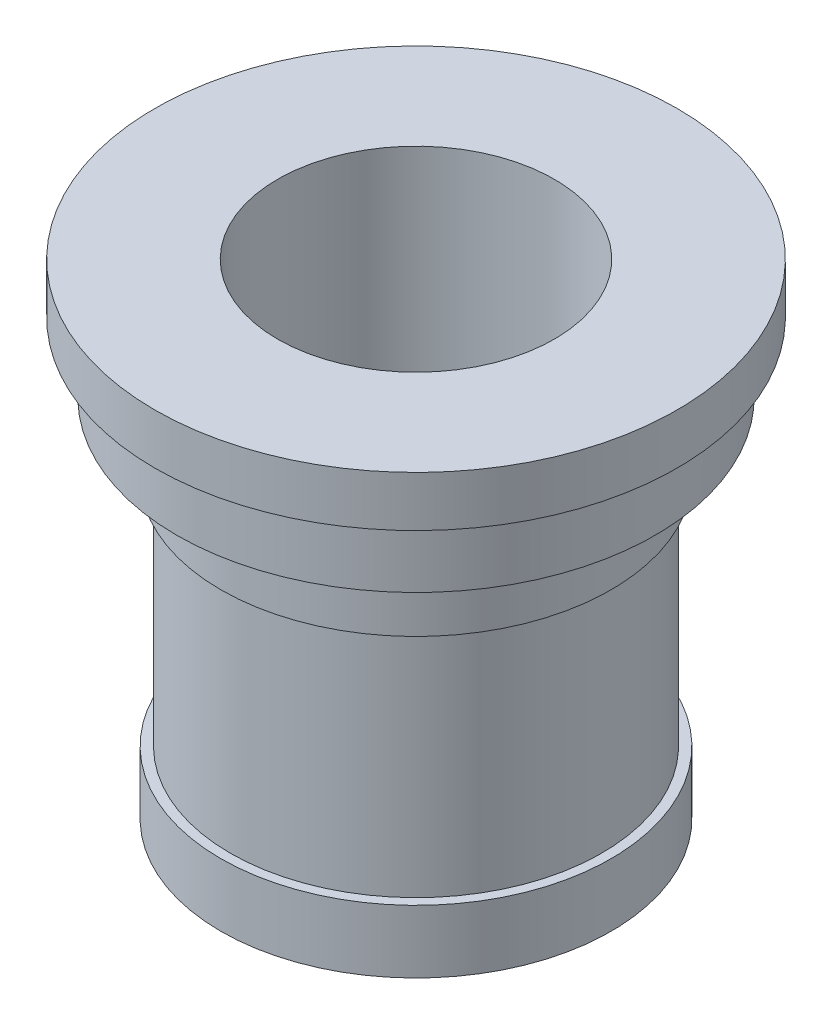
SolidWorks part; units mm, degrees
ref_plane "Front Plane" through (0, 0, 0) normal (0, 0, 1) x (1, 0, 0)
ref_plane "Top Plane" through (0, 0, 0) normal (0, 1, 0) x (1, 0, 0)
ref_plane "Right Plane" through (0, 0, 0) normal (1, 0, 0) x (0, 0, -1)
sketch "Sketch1" plane through (0, 0, 0) normal (0, 1, 0) x (1, 0, 0)
  circle A0 centre (0, 0) radius 31
  dimension "D1" = 62
extrude "Boss-Extrude1" add sketch "Sketch1" along normal blind 10
sketch "Sketch2" plane through (0, 10, 0) normal (0, 1, 0) x (1, 0, 0)
  circle A0 centre (0, 0) radius 29.5
  dimension "D1" = 59
extrude "Boss-Extrude2" add sketch "Sketch2" along normal blind 37
sketch "Sketch4" plane through (0, 47, 0) normal (0, 1, 0) x (1, 0, 0)
  circle A0 centre (0, 0) radius 31
  dimension "D1" = 62
extrude "Boss-Extrude3" add sketch "Sketch4" along normal blind 11
sketch "Sketch5" plane through (0, 58, 0) normal (0, 1, 0) x (1, 0, 0)
  circle A0 centre (0, 0) radius 38
  dimension "D1" = 76
extrude "Boss-Extrude4" add sketch "Sketch5" along normal blind 11
sketch "Sketch6" plane through (0, 69, 0) normal (0, 1, 0) x (1, 0, 0)
  circle A0 centre (0, 0) radius 41.5
  dimension "D1" = 83
extrude "Boss-Extrude5" add sketch "Sketch6" along normal blind 8
sketch "Sketch7" plane through (0, 77, 0) normal (0, 1, 0) x (1, 0, 0)
  circle A0 centre (0, 0) radius 22
  dimension "D1" = 44
extrude "Cut-Extrude1" cut sketch "Sketch7" against normal through all
sketch "Sketch10" plane through (0, 0, 0) normal (0, -1, 0) x (1, 0, 0)
  circle A0 centre (0, 22) radius 1.5
  dimension "D1" = 22
  dimension "D2" = 3
extrude "Cut-Extrude2" cut sketch "Sketch10" against normal blind 5
sketch "Sketch9" plane through (0, 0, 0) normal (0, 0, 1) x (1, 0, 0)
  line L0 (0, 0) -> (-1.3393, 77) construction
  dimension "D1" = 77
